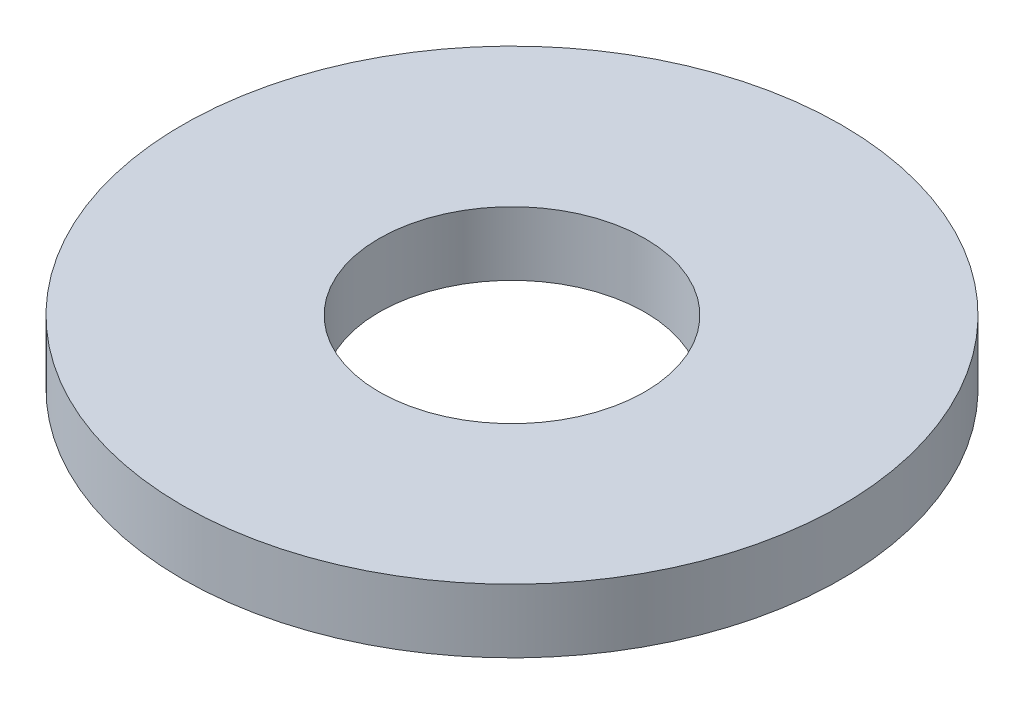
SolidWorks part; units mm, degrees
material "Stainless Steel (ferritic)"
ref_plane "Front Plane" through (0, 0, 0) normal (0, 0, 1) x (1, 0, 0)
ref_plane "Top Plane" through (0, 0, 0) normal (0, 1, 0) x (1, 0, 0)
ref_plane "Right Plane" through (0, 0, 0) normal (1, 0, 0) x (0, 0, -1)
sketch "Sketch1" plane through (0, 0, 0) normal (0, 1, 0) x (1, 0, 0)
  circle A0 centre (0, 0) radius 1.5875
  circle A1 centre (0, 0) radius 3.937
  dimension "D1" = 3.175
  dimension "D2" = 7.874
extrude "Boss-Extrude1" add sketch "Sketch1" along normal blind 0.762
